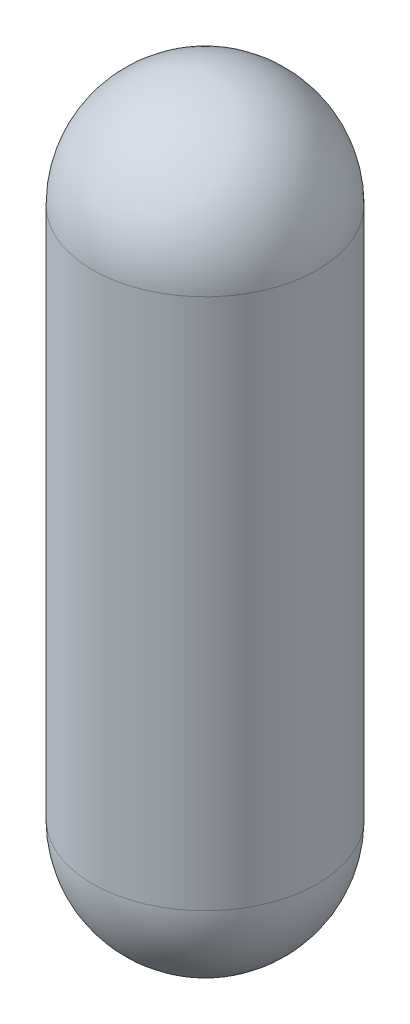
SolidWorks part; units mm, degrees
other "Markup1"
sketch "Sketch2" plane through (-654.05, -2662.4317, 654.05) normal (0, 0, 1) x (1, 0, 0)
material "Titanium"
ref_plane "Front Plane" through (0, 0, 0) normal (0, 0, 1) x (1, 0, 0)
ref_plane "Top Plane" through (0, 0, 0) normal (0, 1, 0) x (1, 0, 0)
ref_plane "Right Plane" through (0, 0, 0) normal (1, 0, 0) x (0, 0, -1)
sketch "Sketch1" plane through (0, 0, 0) normal (0, 0, 1) x (1, 0, 0)
  line L0 (0, 1083.5183) -> (0, 1737.5683)
  line L1 (0, -2008.3817) -> (654.05, -2008.3817) construction
  line L2 (0, -2008.3817) -> (0, 1083.5183)
  line L3 (0, 1083.5183) -> (654.05, 1083.5183) construction
  line L4 (654.05, -2008.3817) -> (654.05, 1083.5183)
  line L5 (0, -2008.3817) -> (0, -2662.4317)
  arc A0 (654.05, 1083.5183) -> (0, 1737.5683) centre (0, 1083.5183) ccw
  arc A1 (654.05, -2008.3817) -> (0, -2662.4317) centre (0, -2008.3817) cw
  dimension "D3" = 654.05
  dimension "D4" = 654.05
  dimension "D1" = 4400
  dimension "D2" = 654.05
revolve "Revolve1" add sketch "Sketch1" angle 360 about L2
